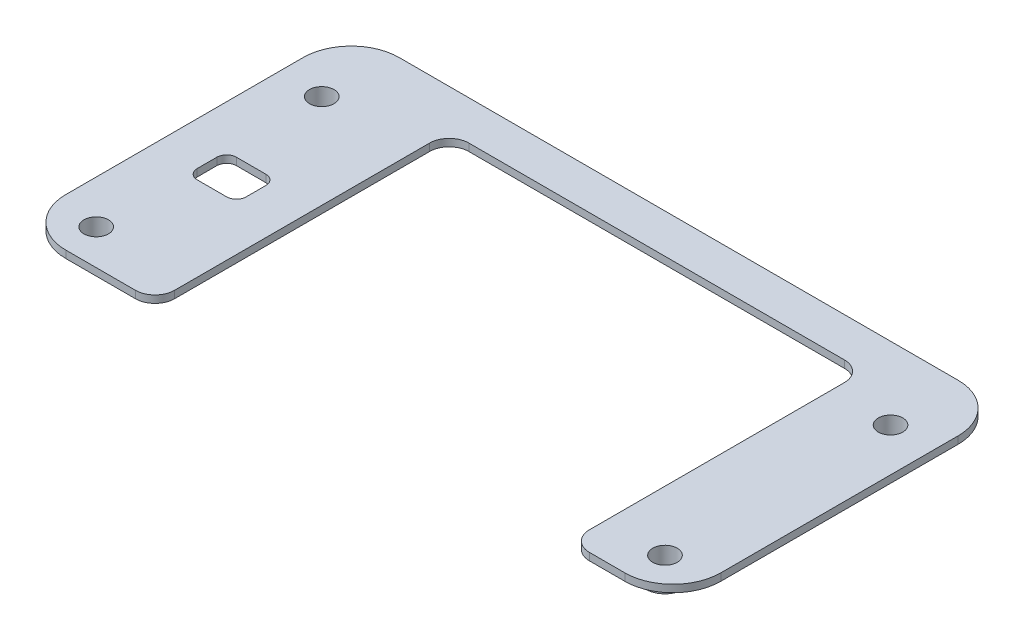
SolidWorks part; units mm, degrees
ref_plane "前视基准面" through (0, 0, 0) normal (0, 0, 1) x (1, 0, 0)
ref_plane "上视基准面" through (0, 0, 0) normal (0, 1, 0) x (1, 0, 0)
ref_plane "右视基准面" through (0, 0, 0) normal (1, 0, 0) x (0, 0, -1)
other "Configuration Table"
sketch "草图1" plane through (0, 0, 0) normal (0, 1, 0) x (1, 0, 0)
  line L0 (-28.2834, 18.335) -> (28.7166, 18.335)
  line L12 (-28.2834, -15.665) -> (-19.7834, -15.665)
  line L13 (-19.7834, -15.665) -> (20.2166, -15.665)
  line L14 (20.2166, -15.665) -> (28.7166, -15.665)
  line L15 (33.6166, -10.765) -> (33.6166, 22.235)
  line L16 (28.7166, 27.135) -> (-28.2834, 27.135)
  line L17 (-33.1834, 22.235) -> (-33.1834, -10.765)
  line L18 (-28.2834, -15.665) -> (-19.7834, -15.665)
  line L19 (-19.7834, -15.665) -> (20.2166, -15.665)
  line L20 (20.2166, -15.665) -> (28.7166, -15.665)
  line L21 (33.6166, -10.765) -> (33.6166, 13.435)
  line L23 (-33.1834, 13.435) -> (-33.1834, -10.765)
  arc A0 (33.6166, 13.435) -> (28.7166, 18.335) centre (28.7166, 13.435) ccw
  arc A1 (-33.1834, 13.435) -> (-28.2834, 18.335) centre (-28.2834, 13.435) cw
  arc A8 (-33.1834, -10.765) -> (-28.2834, -15.665) centre (-28.2834, -10.765) ccw
  arc A9 (28.7166, -15.665) -> (33.6166, -10.765) centre (28.7166, -10.765) ccw
  arc A10 (33.6166, 22.235) -> (28.7166, 27.135) centre (28.7166, 22.235) ccw
  arc A11 (-28.2834, 27.135) -> (-33.1834, 22.235) centre (-28.2834, 22.235) ccw
  arc A12 (-33.1834, -10.765) -> (-28.2834, -15.665) centre (-28.2834, -10.765) ccw
  arc A13 (28.7166, -15.665) -> (33.6166, -10.765) centre (28.7166, -10.765) ccw
  point P9 (-33.1834, 18.335)
  dimension "D3" = 4.9
  dimension "D2" = 34
  dimension "D1" = 0.6
extrude "凸台-拉伸1" add sketch "草图1" along normal blind 0.75
sketch "草图2" plane through (0, 0, 0) normal (0, -1, 0) x (1, 0, 0)
  circle A0 centre (-28.7834, 12.065) radius 2
  circle A1 centre (-28.7834, -10.935) radius 2
  circle A2 centre (29.2166, 12.065) radius 2
  circle A3 centre (29.2166, -10.935) radius 2
  dimension "D1" = 4
extrude "凸台-拉伸2" add sketch "草图2" along normal blind 1.25
sketch "草图3" plane through (0, -1.25, 0) normal (0, -1, 0) x (1, 0, 0)
  circle A0 centre (-28.7834, 12.065) radius 1.25
  circle A1 centre (-28.7834, -10.935) radius 1.25
  circle A2 centre (29.2166, -10.935) radius 1.25
  circle A3 centre (29.2166, 12.065) radius 1.25
extrude "切除-拉伸1" cut sketch "草图3" against normal through all
sketch "草图4" plane through (0, 0.75, 0) normal (0, 1, 0) x (1, 0, 0)
  line L0 (-28.2834, -15.665) -> (28.7166, -15.665) construction
  line L1 (-19.1834, -15.665) -> (23.1166, -15.665)
  line L2 (-19.1834, -15.665) -> (-19.1834, 14.335)
  line L3 (-19.1834, 14.335) -> (23.1166, 14.335)
  line L4 (23.1166, -15.665) -> (23.1166, 14.335)
  line L5 (-33.1834, 13.435) -> (-33.1834, -10.765) construction
  line L6 (33.6166, -10.765) -> (33.6166, 13.435) construction
  point P8 (-19.1834, 14.335)
  point P11 (0, 0)
  dimension "D1" = 14
  dimension "D2" = 30
  dimension "D3" = 10.5
extrude "切除-拉伸2" cut sketch "草图4" against normal through all
fillet "圆角1" radius 2 4 edges at (-19.1834, 0.375, 15.665) (-19.1834, 0.375, -14.335) (23.1166, 0.375, -14.335) (23.1166, 0.375, 15.665)
sketch "草图6" plane through (0, 0, 0) normal (0, -1, 0) x (1, 0, 0)
  line L0 (-28.2834, 15.665) -> (-21.1834, 15.665) construction
  line L2 (-33.1834, -13.435) -> (-33.1834, 10.765) construction
  line L3 (-27.7834, 2.765) -> (-24.7834, 2.765)
  line L4 (-28.7834, 1.765) -> (-28.7834, -0.235)
  line L5 (-27.7834, -1.235) -> (-24.7834, -1.235)
  line L6 (-23.7834, 1.765) -> (-23.7834, -0.235)
  line L7 (-28.7834, 2.765) -> (-23.7834, -1.235) construction
  line L8 (-28.7834, -1.235) -> (-23.7834, 2.765) construction
  arc A0 (-24.7834, 2.765) -> (-23.7834, 1.765) centre (-24.7834, 1.765) cw
  arc A1 (-24.7834, -1.235) -> (-23.7834, -0.235) centre (-24.7834, -0.235) ccw
  arc A2 (-28.7834, -0.235) -> (-27.7834, -1.235) centre (-27.7834, -0.235) ccw
  arc A3 (-27.7834, 2.765) -> (-28.7834, 1.765) centre (-27.7834, 1.765) ccw
  point P0 (-26.2834, 0.765)
  point P5 (-26.3834, 1.0753)
  point P6 (0, 0)
  dimension "D3" = 14.9
  dimension "D5" = 1
  dimension "D1" = 5
  dimension "D2" = 4
  dimension "D4" = 6.9
extrude "切除-拉伸3" cut sketch "草图6" against normal through all
